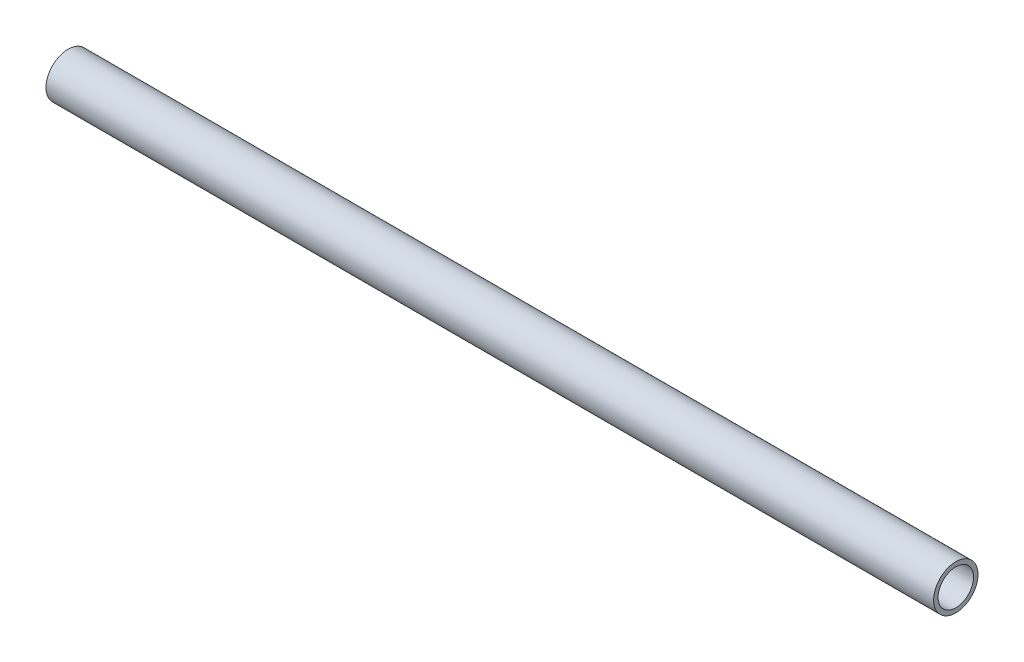
SolidWorks part; units mm, degrees
ref_plane "Front Plane" through (0, 0, 0) normal (0, 0, 1) x (1, 0, 0)
ref_plane "Top Plane" through (0, 0, 0) normal (0, 1, 0) x (1, 0, 0)
ref_plane "Right Plane" through (0, 0, 0) normal (1, 0, 0) x (0, 0, -1)
sketch "Sketch1" plane through (0, 0, 0) normal (1, 0, 0) x (0, 0, -1)
  circle A0 centre (0, 0) radius 5
  circle A1 centre (0, 0) radius 4
  dimension "D1" = 10
  dimension "D2" = 8
extrude "Boss-Extrude1" add sketch "Sketch1" along normal blind 200 contours A0 A1
